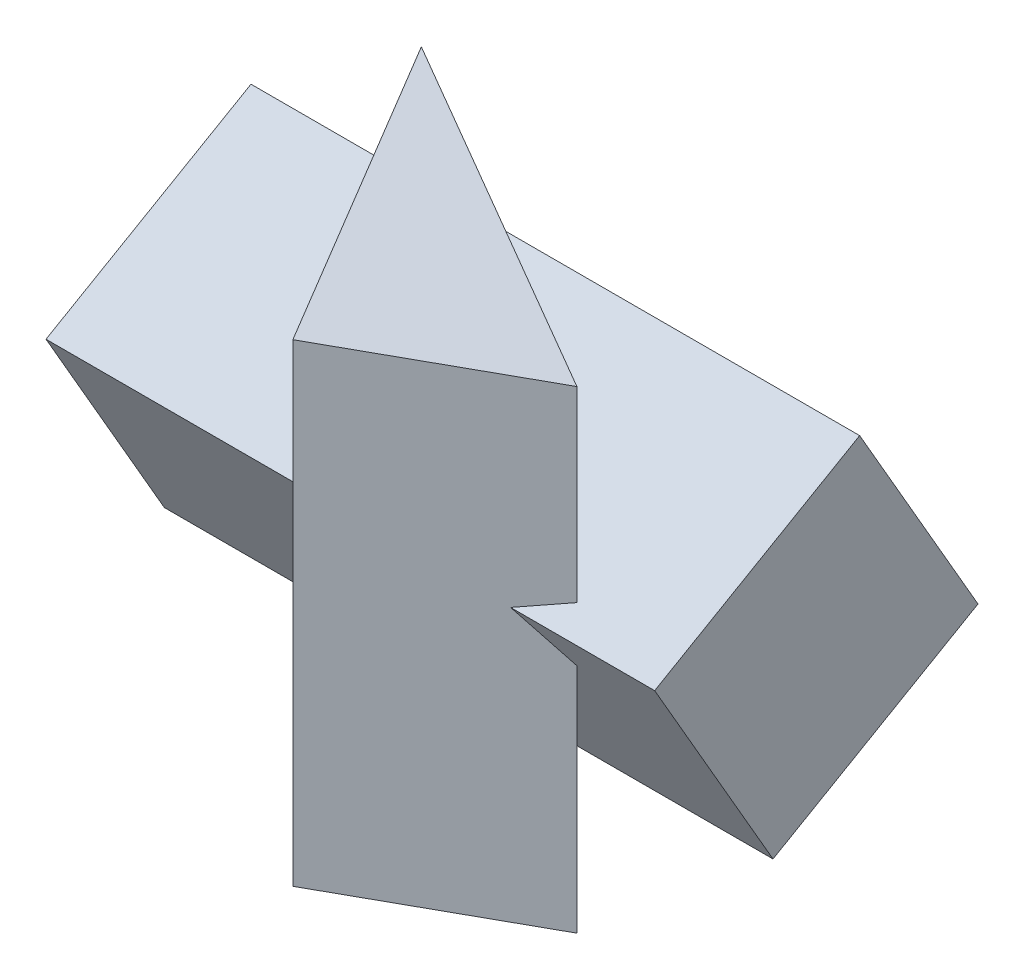
SolidWorks part; units mm, degrees
ref_plane "Front Plane" through (0, 0, 0) normal (0, 0, 1) x (1, 0, 0)
ref_plane "Top Plane" through (0, 0, 0) normal (0, 1, 0) x (1, 0, 0)
ref_plane "Right Plane" through (0, 0, 0) normal (1, 0, 0) x (0, 0, -1)
sketch "Sketch1" plane through (0, 0, 0) normal (0, 1, 0) x (1, 0, 0)
  line L0 (-15, -14) -> (-70, 18)
  line L1 (-70, 18) -> (-42, -29)
  line L2 (-42, -29) -> (-15, -14)
  dimension "D1" = 27
  dimension "D2" = 47
  dimension "D3" = 15
  dimension "D4" = 18
  dimension "D5" = 15
  dimension "D6" = 28
extrude "Triangular prism" add sketch "Sketch1" along normal blind 70
sketch "Sketch2" plane through (0, 0, 0) normal (1, 0, 0) x (0, 0, -1)
  line L0 (12.8109, 57.8109) -> (-17.5, 40.3109)
  line L1 (12.8109, 57.8109) -> (30.3109, 27.5)
  line L2 (-17.5, 40.3109) -> (0, 10)
  line L3 (30.3109, 27.5) -> (0, 10)
  line L4 (18, 0) -> (-29, 0) construction
  dimension "D1" = 35
  dimension "D2" = 35
  dimension "D3" = 10
  dimension "D4" = 30
extrude "Square prism" add sketch "Sketch2" against normal blind 90 contours L0 L2 L3 L1
